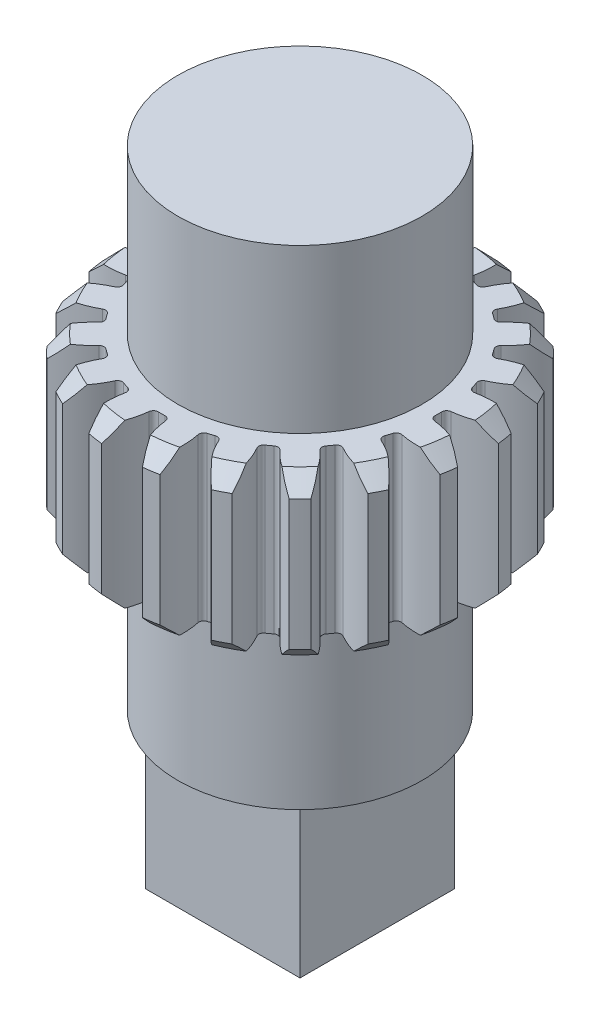
SolidWorks part; units mm, degrees
ref_plane "Front Plane" through (0, 0, 0) normal (0, 0, 1) x (1, 0, 0)
ref_plane "Top Plane" through (0, 0, 0) normal (0, 1, 0) x (1, 0, 0)
ref_plane "Right Plane" through (0, 0, 0) normal (1, 0, 0) x (0, 0, -1)
sketch "Sketch1" plane through (0, 0, 0) normal (0, 1, 0) x (1, 0, 0)
  circle A0 centre (0, 0) radius 10 construction
  circle A1 centre (0, 0) radius 11
  dimension "D1" = 20
  dimension "D2" = 22
extrude "Boss-Extrude1" add sketch "Sketch1" along normal mid plane 10
sketch "Sketch2" plane through (0, 0, 0) normal (0, 1, 0) x (1, 0, 0)
  line L0 (0, 11) -> (0, 0) construction
  line L1 (0, 0) -> (1.7208, 10.8646) construction
  line L2 (0, 0) -> (3.3992, 10.4616) construction
  line L3 (-0.4798, 8.4865) -> (0, 0) construction
  line L4 (-0.7846, 9.9692) -> (0.7846, 9.9692) construction
  line L5 (0.7846, 9.9692) -> (2.3345, 9.7237) construction
  line L6 (-1.1383, 10.9409) -> (0, 7.8135) construction
  circle A0 centre (0, 0) radius 9 construction
  circle A2 centre (0, 0) radius 11 construction
  arc A3 (-1.2504, 10.9287) -> (-0.4798, 8.4865) centre (-5.6635, 8.1934) cw
  arc A4 (1.2504, 10.9287) -> (0.4798, 8.4865) centre (5.6635, 8.1934) ccw
  circle A5 centre (0, 0) radius 10 construction
  arc A6 (0.4798, 8.4865) -> (-0.4798, 8.4865) centre (0, 0) ccw
  arc A7 (-1.2504, 10.9287) -> (1.2504, 10.9287) centre (0, 0) cw
  dimension "D1" = 18
  dimension "D2" = 9
  dimension "D4" = 2
  dimension "D5" = 20
  dimension "D3" = 0.5
extrude "Cut-Extrude4" cut sketch "Sketch2" against normal through all both and the other way through all
fillet "Fillet1" radius 0.3 2 edges at (0.4798, 0, -8.4865) (-0.4798, 0, -8.4865)
chamfer "Chamfer1" distance 1 angle 45 2 edges at (0, 5, 11) (0, -5, 11)
pattern_circular "CirPattern1" count 20 over 360 about axis through (0, 0, 0) along (0, 1, 0) of "Fillet1", "Cut-Extrude4"
sketch "Sketch3" plane through (0, 5, 0) normal (0, 1, 0) x (1, 0, 0)
  circle A0 centre (0, 0) radius 7.5
  dimension "D1" = 15
extrude "Boss-Extrude2" add sketch "Sketch3" along normal blind 10
sketch "Sketch6" plane through (0, -5, 0) normal (0, -1, 0) x (1, 0, 0)
  circle A0 centre (0, 0) radius 7.5
  dimension "D1" = 15
extrude "Boss-Extrude3" add sketch "Sketch6" along normal blind 10
sketch "Sketch7" plane through (0, -15, 0) normal (0, -1, 0) x (1, 0, 0)
  line L1 (-4.75, 4.75) -> (4.75, 4.75)
  line L2 (-4.75, 4.75) -> (-4.75, -4.75)
  line L3 (-4.75, -4.75) -> (4.75, -4.75)
  line L4 (4.75, 4.75) -> (4.75, -4.75)
  line L5 (-4.75, 4.75) -> (4.75, -4.75) construction
  line L6 (-4.75, -4.75) -> (4.75, 4.75) construction
  point P0 (0, 0)
  dimension "D1" = 9.5
  dimension "D2" = 9.5
extrude "Boss-Extrude4" add sketch "Sketch7" along normal blind 9.5
equation "\"D1@Sketch1\" = \"Module\" * \"Number of Teeth\""
equation "\"D2@Sketch1\" = ( \"Number of Teeth\" + 2 ) * \"Module\""
equation "\"D1@Sketch2\" = 360 / \"Number of Teeth\""
equation "\"D2@Sketch2\" = 180 / \"Number of Teeth\""
equation "\"D4@Sketch2\" = \"Module\" * 2"
equation "\"D5@Sketch2\"= \"Pressure Angle\""
equation "\"D1@Fillet1\" = 0.3 * \"Module\""
equation "\"D1@CirPattern1\" = \"Number of Teeth\""
equation "\"D1@Chamfer1\" = \"Module\""
